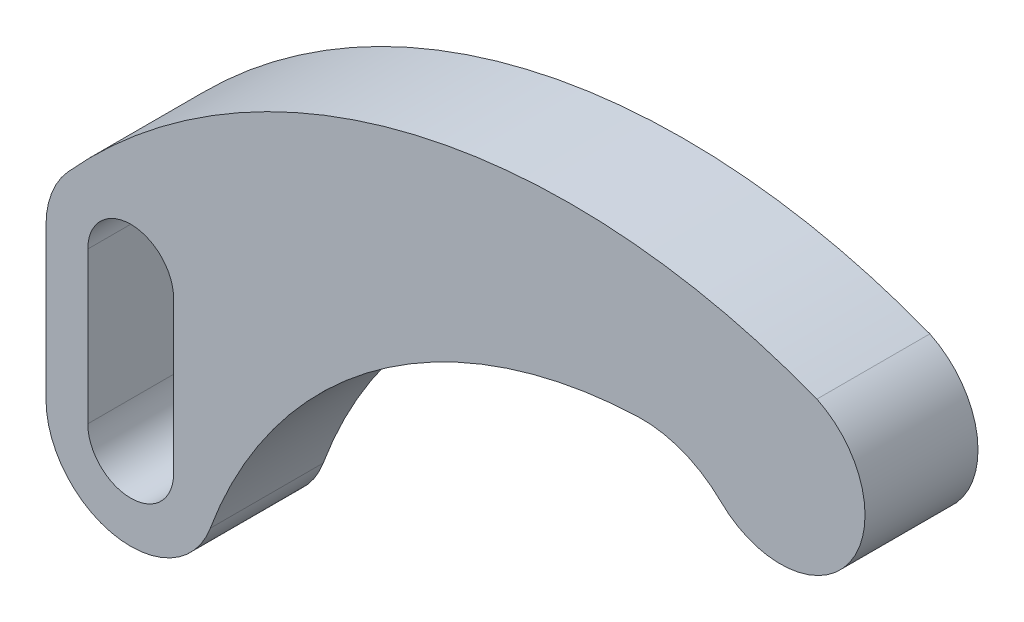
SolidWorks part; units mm, degrees
ref_plane "Front Plane" through (0, 0, 0) normal (0, 0, 1) x (1, 0, 0)
ref_plane "Top Plane" through (0, 0, 0) normal (0, 1, 0) x (1, 0, 0)
ref_plane "Right Plane" through (0, 0, 0) normal (1, 0, 0) x (0, 0, -1)
sketch "Sketch2" plane through (0, 0, 0) normal (0, 0, 1) x (1, 0, 0)
  line L0 (-147.9441, -6.4294) -> (-147.9441, -40.4654)
  line L1 (-128.6401, -6.4294) -> (-128.6401, -40.4654)
  line L2 (-157.3421, -40.4654) -> (-157.3421, -6.4294)
  arc A0 (-5.5744, 15.5234) -> (12.9096, 47.4707) centre (7.7579, 29.1306) ccw
  arc A3 (-128.6401, -6.4294) -> (-147.9441, -6.4294) centre (-138.2921, -6.4294) ccw
  arc A4 (-147.9441, -40.4654) -> (-128.6401, -40.4654) centre (-138.2921, -40.4654) ccw
  arc A7 (-157.3421, -40.4654) -> (-120.4117, -47.0375) centre (-138.2921, -40.4654) ccw
  arc A8 (-152.4405, 6.327) -> (-157.3421, -6.4294) centre (-138.2921, -6.4294) ccw
  arc A9 (15.9817, 46.314) -> (-152.4405, 6.327) centre (-39.2534, -95.7242) ccw
  arc A10 (-5.5744, 15.5234) -> (-24.3098, 22.7625) centre (-23.3507, -2.6194) ccw
  arc A11 (-24.3098, 22.7625) -> (-120.4117, -47.0375) centre (-20.2813, -83.8414) ccw
  point P18 (-157.3421, -6.7293)
  point P20 (13.8525, 47.1237)
  dimension "D1" = 146.05
  dimension "D4" = 106.68
  dimension "D8" = 152.4
  dimension "D5" = 25.4
  dimension "D7" = 19.05
  dimension "D9" = 19.05
  dimension "D10" = 9.652
  dimension "D2" = 69.596
  dimension "D3" = 34.036
  dimension "D6" = 31.75
extrude "Boss-Extrude1" add sketch "Sketch2" along normal blind 25.4 contours A11 A10 A0 A9 A8 L2 A7 A4 L0 A3 L1
